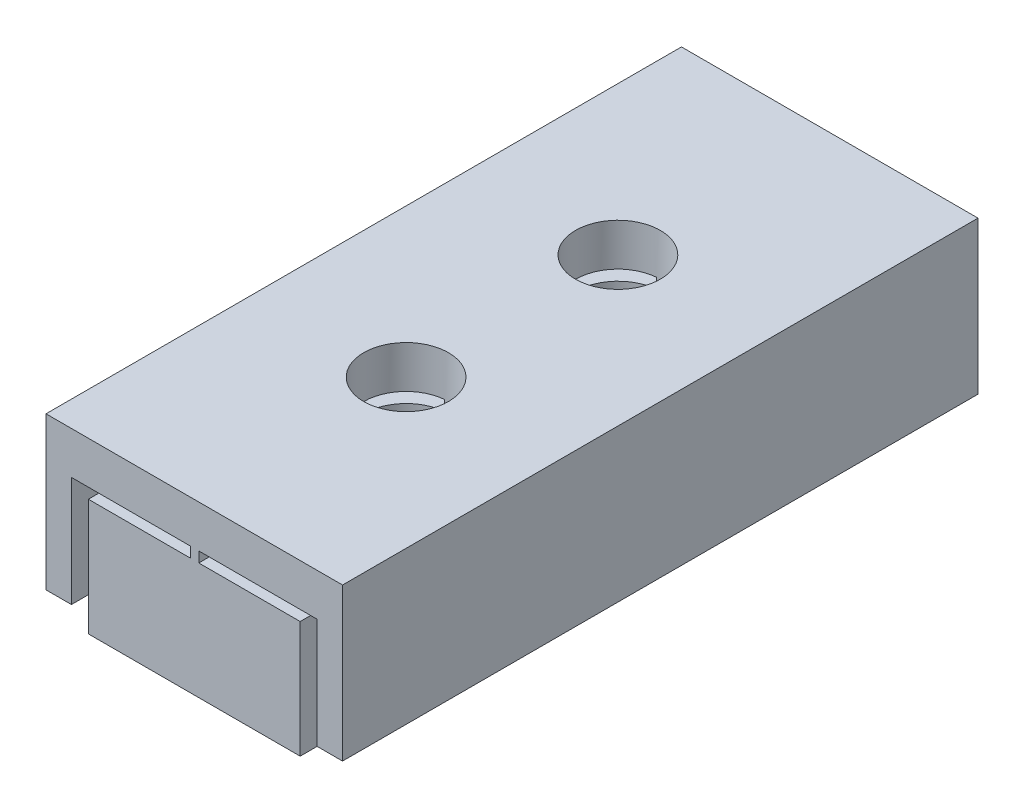
SolidWorks part; units mm, degrees
ref_plane "前视基准面" through (0, 0, 0) normal (0, 0, 1) x (1, 0, 0)
ref_plane "上视基准面" through (0, 0, 0) normal (0, 1, 0) x (1, 0, 0)
ref_plane "右视基准面" through (0, 0, 0) normal (1, 0, 0) x (0, 0, -1)
sketch "草图1" plane through (0, 0, 0) normal (0, 1, 0) x (1, 0, 0)
  line L1 (0, 0) -> (-5, 0)
  line L2 (0, 0) -> (0, -15)
  line L3 (0, -15) -> (-5, -15)
  line L4 (-5, 0) -> (-5, -15)
  dimension "D1" = 5
  dimension "D2" = 15
extrude "凸台-拉伸1" add sketch "草图1" along normal blind 3
sketch "草图2" plane through (0, 0, 0) normal (0, 0, -1) x (-1, 0, 0)
  line L0 (-0.4, 0) -> (-0.4, 3)
  line L1 (-0.4, 3) -> (5.4, 3)
  line L2 (5.4, 3) -> (5.4, 0)
  line L3 (5.4, 0) -> (6, 0)
  line L4 (6, 0) -> (6, 4)
  line L5 (6, 4) -> (-1, 4)
  line L6 (-1, 4) -> (-1, 0)
  line L7 (-1, 0) -> (-0.4, 0)
  line L8 (-0.4, 1.5) -> (0, 1.5) construction
  line L9 (0, 3) -> (0, 0) construction
  line L10 (5, 1.5) -> (5.4, 1.5) construction
  line L11 (5, 3) -> (5, 0) construction
  dimension "D1" = 7
  dimension "D2" = 4
  dimension "D3" = 0.4
extrude "凸台-拉伸2" add sketch "草图2" against normal blind 15
sketch "草图3" plane through (0, 4, 0) normal (0, 1, 0) x (1, 0, 0)
  line L0 (-2.5, -15) -> (-2.5, -10) construction
  line L1 (-6, -15) -> (1, -15) construction
  line L2 (-2.5, -5) -> (-2.5, 0) construction
  line L3 (-6, 0) -> (1, 0) construction
  circle A0 centre (-2.5, -10) radius 1
  circle A1 centre (-2.5, -5) radius 1
  dimension "D2" = 2
  dimension "D1" = 5
extrude "切除-拉伸1" cut sketch "草图3" against normal through all
sketch "草图5" plane through (0, 0, 15) normal (0, 0, 1) x (1, 0, 0)
  line L1 (-5, 3) -> (-2.5904, 3)
  line L2 (-5, 3) -> (-5, 2.7536)
  line L3 (-5, 2.7536) -> (-2.5904, 2.7536)
  line L4 (-2.5904, 3) -> (-2.5904, 2.7536)
  line L5 (0, 3) -> (-2.3933, 3)
  line L6 (0, 3) -> (0, 2.7536)
  line L7 (0, 2.7536) -> (-2.3933, 2.7536)
  line L8 (-2.3933, 3) -> (-2.3933, 2.7536)
extrude "切除-拉伸3" cut sketch "草图5" against normal blind 15
sketch "草图6" plane through (0, 0, 0) normal (0, 0, -1) x (-1, 0, 0)
  line L0 (-1, 4) -> (-1, 0) construction
  line L1 (-0.4, 0) -> (-1, 0)
  line L2 (-0.4, 0) -> (-0.4, 0.4)
  line L3 (-0.4, 0.4) -> (-1, 0.4)
  line L4 (-1, 0) -> (-1, 0.4)
  line L5 (5.4, 3) -> (5.4, 0) construction
  line L6 (6, 0) -> (5.4, 0)
  line L7 (6, 0) -> (6, 0.4)
  line L8 (6, 0.4) -> (5.4, 0.4)
  line L9 (5.4, 0) -> (5.4, 0.4)
  dimension "D1" = 0.4
extrude "切除-拉伸4" cut sketch "草图6" against normal blind 15
